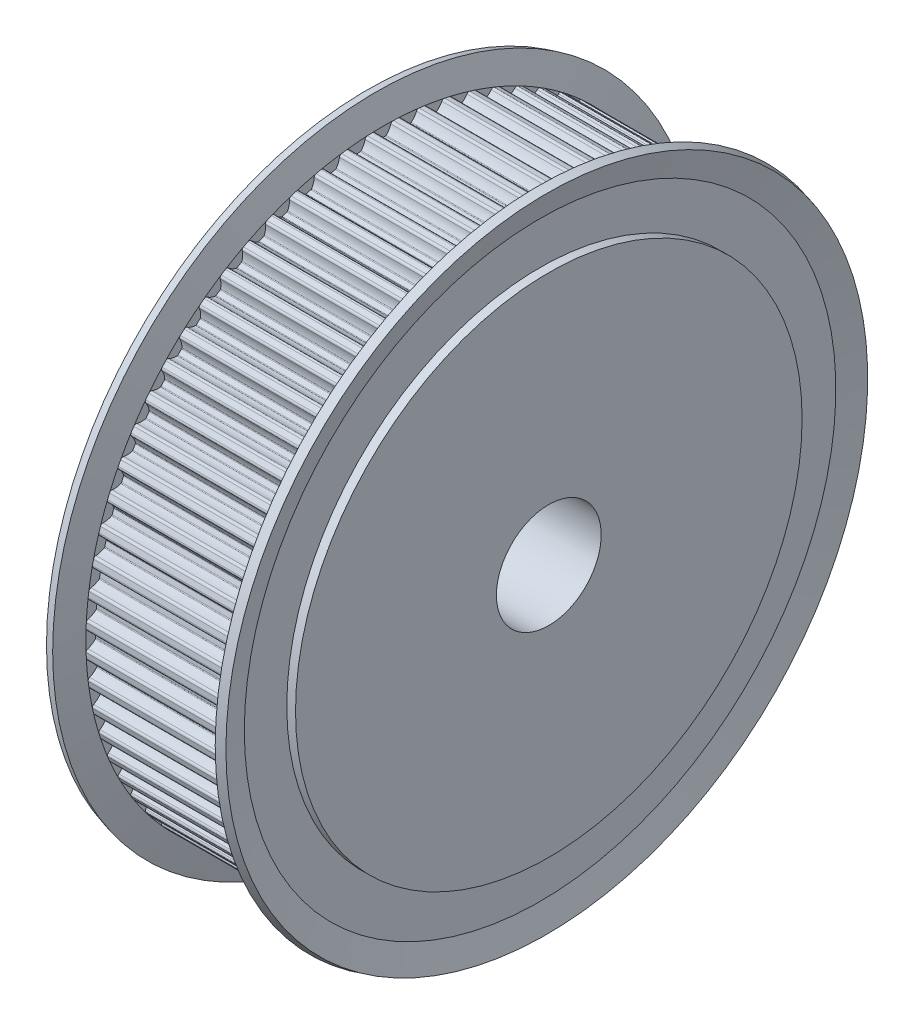
SolidWorks part; units mm, degrees
ref_plane "正面" through (0, 0, 0) normal (0, 0, 1) x (1, 0, 0)
ref_plane "平面" through (0, 0, 0) normal (0, 1, 0) x (1, 0, 0)
ref_plane "右側面" through (0, 0, 0) normal (1, 0, 0) x (0, 0, -1)
ref_plane "平面1" through (0, 0, 0) normal (0, 0, 1) x (1, 0, 0)
sketch "ｽｹｯﾁ1" plane through (0, 0, 0) normal (0, 0, 1) x (1, 0, 0)
  line L0 (0, 0) -> (0, 29)
  line L1 (0, 29) -> (1, 29)
  line L2 (1, 29) -> (1, 33.8633)
  line L3 (1, 33.8633) -> (0.2289, 36.7412)
  line L4 (0.2289, 36.7412) -> (1.1948, 37)
  line L5 (1.1948, 37) -> (2, 33.995)
  line L6 (2, 33.995) -> (19, 33.995)
  line L7 (19, 33.995) -> (19.8052, 37)
  line L8 (19.8052, 37) -> (20.7711, 36.7412)
  line L9 (20.7711, 36.7412) -> (20, 33.8633)
  line L10 (20, 33.8633) -> (20, 29)
  line L11 (20, 29) -> (21, 29)
  line L12 (21, 29) -> (21, 0)
  line L13 (21, 0) -> (0, 0)
  line L14 (21, 0) -> (0, 0) construction
revolve "回転1" add sketch "ｽｹｯﾁ1" angle 360 about L14
ref_plane "平面2" through (0, 0, 0) normal (0, 0, 1) x (1, 0, 0)
sketch "ｽｹｯﾁ2" plane through (0, 0, 0) normal (0, 0, 1) x (1, 0, 0)
  line L0 (0, 0) -> (0, 6)
  line L1 (0, 6) -> (21, 6)
  line L2 (21, 6) -> (21, 0)
  line L3 (21, 0) -> (0, 0)
  line L4 (21, 0) -> (0, 0) construction
revolve "ｶｯﾄ - 回転1" cut sketch "ｽｹｯﾁ2" angle 360 about L4
ref_plane "平面3" through (2, 0, 0) normal (1, 0, 0) x (0, 0, -1)
sketch "ｽｹｯﾁ3" plane through (2, 0, 0) normal (1, 0, 0) x (0, 0, -1)
  circle A0 centre (0, 0) radius 38.995
  arc A1 (-33.7772, -0.9117) -> (-33.9742, -1.189) centre (-33.6944, -1.1792) ccw
  arc A2 (-33.9742, -1.189) -> (-33.9485, -1.7766) centre (0, 0) ccw
  arc A3 (-33.9485, -1.7766) -> (-33.7281, -2.0357) centre (-33.6689, -1.762) ccw
  arc A4 (-33.7281, -2.0357) -> (-32.8326, -2.4906) centre (-34.1454, -3.9661) cw
  arc A5 (-32.8326, -2.4906) -> (-32.7828, -2.5908) centre (-32.9323, -2.6026) cw
  arc A6 (-32.7828, -2.5908) -> (-32.7346, -3.1412) centre (0, 0) ccw
  arc A7 (-32.7346, -3.1412) -> (-32.7663, -3.2486) centre (-32.8839, -3.1556) cw
  arc A8 (-32.7663, -3.2486) -> (-33.5692, -3.8521) centre (-34.3154, -2.0235) cw
  arc A9 (-33.5692, -3.8521) -> (-33.7413, -4.1455) centre (-33.4634, -4.1113) ccw
  arc A10 (-33.7413, -4.1455) -> (-33.6645, -4.7287) centre (0, 0) ccw
  arc A11 (-33.6645, -4.7287) -> (-33.4223, -4.9675) centre (-33.3872, -4.6897) ccw
  arc A12 (-33.4223, -4.9675) -> (-32.4906, -5.3426) centre (-33.6698, -6.9269) cw
  arc A13 (-32.4906, -5.3426) -> (-32.4322, -5.4382) centre (-32.5802, -5.463) cw
  arc A14 (-32.4322, -5.4382) -> (-32.3363, -5.9823) centre (0, 0) ccw
  arc A15 (-32.3363, -5.9823) -> (-32.3585, -6.092) centre (-32.4838, -6.0096) cw
  arc A16 (-32.3585, -6.092) -> (-33.1057, -6.7632) centre (-34.0085, -5.0066) cw
  arc A17 (-33.1057, -6.7632) -> (-33.2516, -7.0704) centre (-32.9777, -7.0122) ccw
  arc A18 (-33.2516, -7.0704) -> (-33.1243, -7.6447) centre (0, 0) ccw
  arc A19 (-33.1243, -7.6447) -> (-32.8622, -7.8616) centre (-32.8515, -7.5818) ccw
  arc A20 (-32.8622, -7.8616) -> (-31.9013, -8.154) centre (-32.938, -9.8351) cw
  arc A21 (-31.9013, -8.154) -> (-31.8349, -8.2441) centre (-31.9801, -8.2817) cw
  arc A22 (-31.8349, -8.2441) -> (-31.6918, -8.7778) centre (0, 0) ccw
  arc A23 (-31.6918, -8.7778) -> (-31.7044, -8.8891) centre (-31.8364, -8.8178) cw
  arc A24 (-31.7044, -8.8891) -> (-32.3903, -9.6228) centre (-33.4427, -7.9515) cw
  arc A25 (-32.3903, -9.6228) -> (-32.5088, -9.9416) centre (-32.2411, -9.8597) ccw
  arc A26 (-32.5088, -9.9416) -> (-32.332, -10.5026) centre (0, 0) ccw
  arc A27 (-32.332, -10.5026) -> (-32.052, -10.6958) centre (-32.0657, -10.4161) ccw
  arc A28 (-32.052, -10.6958) -> (-31.0693, -10.9034) centre (-31.9555, -12.6684) cw
  arc A29 (-31.0693, -10.9034) -> (-30.9952, -10.9873) centre (-31.1366, -11.0375) cw
  arc A30 (-30.9952, -10.9873) -> (-30.8062, -11.5065) centre (0, 0) ccw
  arc A31 (-30.8062, -11.5065) -> (-30.809, -11.6184) centre (-30.9467, -11.559) cw
  arc A32 (-30.809, -11.6184) -> (-31.4283, -12.4092) centre (-32.6224, -10.836) cw
  arc A33 (-31.4283, -12.4092) -> (-31.5187, -12.7371) centre (-31.2591, -12.6322) ccw
  arc A34 (-31.5187, -12.7371) -> (-31.2936, -13.2806) centre (0, 0) ccw
  arc A35 (-31.2936, -13.2806) -> (-30.9978, -13.4486) centre (-31.0358, -13.1712) ccw
  arc A36 (-30.9978, -13.4486) -> (-30.0007, -13.5698) centre (-30.7297, -15.4053) cw
  arc A37 (-30.0007, -13.5698) -> (-29.9196, -13.6469) centre (-30.0561, -13.7092) cw
  arc A38 (-29.9196, -13.6469) -> (-29.6861, -14.1477) centre (0, 0) ccw
  arc A39 (-29.6861, -14.1477) -> (-29.6792, -14.2594) centre (-29.8215, -14.2122) cw
  arc A40 (-29.6792, -14.2594) -> (-30.2272, -15.1011) centre (-31.5538, -13.638) cw
  arc A41 (-30.2272, -15.1011) -> (-30.2886, -15.4357) centre (-30.0391, -15.3085) ccw
  arc A42 (-30.2886, -15.4357) -> (-30.017, -15.9574) centre (0, 0) ccw
  arc A43 (-30.017, -15.9574) -> (-29.7077, -16.099) centre (-29.7698, -15.826) ccw
  arc A44 (-29.7077, -16.099) -> (-28.7039, -16.1329) centre (-29.2701, -18.025) cw
  arc A45 (-28.7039, -16.1329) -> (-28.6164, -16.2027) centre (-28.7469, -16.2766) cw
  arc A46 (-28.6164, -16.2027) -> (-28.3401, -16.6812) centre (0, 0) ccw
  arc A47 (-28.3401, -16.6812) -> (-28.3234, -16.7919) centre (-28.4694, -16.7573) cw
  arc A48 (-28.3234, -16.7919) -> (-28.796, -17.6781) centre (-30.2451, -16.3362) cw
  arc A49 (-28.796, -17.6781) -> (-28.828, -18.0168) centre (-28.5906, -17.8684) ccw
  arc A50 (-28.828, -18.0168) -> (-28.512, -18.5129) centre (0, 0) ccw
  arc A51 (-28.512, -18.5129) -> (-28.1916, -18.627) centre (-28.2772, -18.3604) ccw
  arc A52 (-28.1916, -18.627) -> (-27.1886, -18.5732) centre (-27.5878, -20.5074) cw
  arc A53 (-27.1886, -18.5732) -> (-27.0953, -18.6351) centre (-27.2189, -18.7201) cw
  arc A54 (-27.0953, -18.6351) -> (-26.7784, -19.0877) centre (0, 0) ccw
  arc A55 (-26.7784, -19.0877) -> (-26.7521, -19.1965) centre (-26.9006, -19.1748) cw
  arc A56 (-26.7521, -19.1965) -> (-27.1457, -20.1206) centre (-28.7063, -18.9101) cw
  arc A57 (-27.1457, -20.1206) -> (-27.1481, -20.4607) centre (-26.9245, -20.2922) ccw
  arc A58 (-27.1481, -20.4607) -> (-26.79, -20.9274) centre (0, 0) ccw
  arc A59 (-26.79, -20.9274) -> (-26.4608, -21.0132) centre (-26.5693, -20.755) ccw
  arc A60 (-26.4608, -21.0132) -> (-25.4664, -20.8722) centre (-25.6955, -22.8338) cw
  arc A61 (-25.4664, -20.8722) -> (-25.3681, -20.9257) centre (-25.4838, -21.0211) cw
  arc A62 (-25.3681, -20.9257) -> (-25.0129, -21.349) centre (0, 0) ccw
  arc A63 (-25.0129, -21.349) -> (-24.9773, -21.4551) centre (-25.127, -21.4463) cw
  arc A64 (-24.9773, -21.4551) -> (-25.2888, -22.4099) centre (-26.9489, -21.34) cw
  arc A65 (-25.2888, -22.4099) -> (-25.2615, -22.749) centre (-25.0534, -22.5616) ccw
  arc A66 (-25.2615, -22.749) -> (-24.8641, -23.1827) centre (0, 0) ccw
  arc A67 (-24.8641, -23.1827) -> (-24.5287, -23.2394) centre (-24.6593, -22.9917) ccw
  arc A68 (-24.5287, -23.2394) -> (-23.5503, -23.0123) centre (-23.6076, -24.9864) cw
  arc A69 (-23.5503, -23.0123) -> (-23.4477, -23.057) centre (-23.5547, -23.1622) cw
  arc A70 (-23.4477, -23.057) -> (-23.057, -23.4477) centre (0, 0) ccw
  arc A71 (-23.057, -23.4477) -> (-23.0123, -23.5503) centre (-23.1622, -23.5547) cw
  arc A72 (-23.0123, -23.5503) -> (-23.2394, -24.5287) centre (-24.9864, -23.6076) cw
  arc A73 (-23.2394, -24.5287) -> (-23.1827, -24.8641) centre (-22.9917, -24.6593) ccw
  arc A74 (-23.1827, -24.8641) -> (-22.749, -25.2615) centre (0, 0) ccw
  arc A75 (-22.749, -25.2615) -> (-22.4099, -25.2888) centre (-22.5616, -25.0534) ccw
  arc A76 (-22.4099, -25.2888) -> (-21.4551, -24.9773) centre (-21.34, -26.9489) cw
  arc A77 (-21.4551, -24.9773) -> (-21.349, -25.0129) centre (-21.4463, -25.127) cw
  arc A78 (-21.349, -25.0129) -> (-20.9257, -25.3681) centre (0, 0) ccw
  arc A79 (-20.9257, -25.3681) -> (-20.8722, -25.4664) centre (-21.0211, -25.4838) cw
  arc A80 (-20.8722, -25.4664) -> (-21.0132, -26.4608) centre (-22.8338, -25.6955) cw
  arc A81 (-21.0132, -26.4608) -> (-20.9274, -26.79) centre (-20.755, -26.5693) ccw
  arc A82 (-20.9274, -26.79) -> (-20.4607, -27.1481) centre (0, 0) ccw
  arc A83 (-20.4607, -27.1481) -> (-20.1206, -27.1457) centre (-20.2922, -26.9245) ccw
  arc A84 (-20.1206, -27.1457) -> (-19.1965, -26.7521) centre (-18.9101, -28.7063) cw
  arc A85 (-19.1965, -26.7521) -> (-19.0877, -26.7784) centre (-19.1748, -26.9006) cw
  arc A86 (-19.0877, -26.7784) -> (-18.6351, -27.0953) centre (0, 0) ccw
  arc A87 (-18.6351, -27.0953) -> (-18.5732, -27.1886) centre (-18.7201, -27.2189) cw
  arc A88 (-18.5732, -27.1886) -> (-18.627, -28.1916) centre (-20.5074, -27.5878) cw
  arc A89 (-18.627, -28.1916) -> (-18.5129, -28.512) centre (-18.3604, -28.2772) ccw
  arc A90 (-18.5129, -28.512) -> (-18.0168, -28.828) centre (0, 0) ccw
  arc A91 (-18.0168, -28.828) -> (-17.6781, -28.796) centre (-17.8684, -28.5906) ccw
  arc A92 (-17.6781, -28.796) -> (-16.7919, -28.3234) centre (-16.3362, -30.2451) cw
  arc A93 (-16.7919, -28.3234) -> (-16.6812, -28.3401) centre (-16.7573, -28.4694) cw
  arc A94 (-16.6812, -28.3401) -> (-16.2027, -28.6164) centre (0, 0) ccw
  arc A95 (-16.2027, -28.6164) -> (-16.1329, -28.7039) centre (-16.2766, -28.7469) cw
  arc A96 (-16.1329, -28.7039) -> (-16.099, -29.7077) centre (-18.025, -29.2701) cw
  arc A97 (-16.099, -29.7077) -> (-15.9574, -30.017) centre (-15.826, -29.7698) ccw
  arc A98 (-15.9574, -30.017) -> (-15.4357, -30.2886) centre (0, 0) ccw
  arc A99 (-15.4357, -30.2886) -> (-15.1011, -30.2272) centre (-15.3085, -30.0391) ccw
  arc A100 (-15.1011, -30.2272) -> (-14.2594, -29.6792) centre (-13.638, -31.5538) cw
  arc A101 (-14.2594, -29.6792) -> (-14.1477, -29.6861) centre (-14.2122, -29.8215) cw
  arc A102 (-14.1477, -29.6861) -> (-13.6469, -29.9196) centre (0, 0) ccw
  arc A103 (-13.6469, -29.9196) -> (-13.5698, -30.0007) centre (-13.7092, -30.0561) cw
  arc A104 (-13.5698, -30.0007) -> (-13.4486, -30.9978) centre (-15.4053, -30.7297) cw
  arc A105 (-13.4486, -30.9978) -> (-13.2806, -31.2936) centre (-13.1712, -31.0358) ccw
  arc A106 (-13.2806, -31.2936) -> (-12.7371, -31.5187) centre (0, 0) ccw
  arc A107 (-12.7371, -31.5187) -> (-12.4092, -31.4283) centre (-12.6322, -31.2591) ccw
  arc A108 (-12.4092, -31.4283) -> (-11.6184, -30.809) centre (-10.836, -32.6224) cw
  arc A109 (-11.6184, -30.809) -> (-11.5065, -30.8062) centre (-11.559, -30.9467) cw
  arc A110 (-11.5065, -30.8062) -> (-10.9873, -30.9952) centre (0, 0) ccw
  arc A111 (-10.9873, -30.9952) -> (-10.9034, -31.0693) centre (-11.0375, -31.1366) cw
  arc A112 (-10.9034, -31.0693) -> (-10.6958, -32.052) centre (-12.6684, -31.9555) cw
  arc A113 (-10.6958, -32.052) -> (-10.5026, -32.332) centre (-10.4161, -32.0657) ccw
  arc A114 (-10.5026, -32.332) -> (-9.9416, -32.5088) centre (0, 0) ccw
  arc A115 (-9.9416, -32.5088) -> (-9.6228, -32.3903) centre (-9.8597, -32.2411) ccw
  arc A116 (-9.6228, -32.3903) -> (-8.8891, -31.7044) centre (-7.9515, -33.4427) cw
  arc A117 (-8.8891, -31.7044) -> (-8.7778, -31.6918) centre (-8.8178, -31.8364) cw
  arc A118 (-8.7778, -31.6918) -> (-8.2441, -31.8349) centre (0, 0) ccw
  arc A119 (-8.2441, -31.8349) -> (-8.154, -31.9013) centre (-8.2817, -31.9801) cw
  arc A120 (-8.154, -31.9013) -> (-7.8616, -32.8622) centre (-9.8351, -32.938) cw
  arc A121 (-7.8616, -32.8622) -> (-7.6447, -33.1243) centre (-7.5818, -32.8515) ccw
  arc A122 (-7.6447, -33.1243) -> (-7.0704, -33.2516) centre (0, 0) ccw
  arc A123 (-7.0704, -33.2516) -> (-6.7632, -33.1057) centre (-7.0122, -32.9777) ccw
  arc A124 (-6.7632, -33.1057) -> (-6.092, -32.3585) centre (-5.0066, -34.0085) cw
  arc A125 (-6.092, -32.3585) -> (-5.9823, -32.3363) centre (-6.0096, -32.4838) cw
  arc A126 (-5.9823, -32.3363) -> (-5.4382, -32.4322) centre (0, 0) ccw
  arc A127 (-5.4382, -32.4322) -> (-5.3426, -32.4906) centre (-5.463, -32.5802) cw
  arc A128 (-5.3426, -32.4906) -> (-4.9675, -33.4223) centre (-6.9269, -33.6698) cw
  arc A129 (-4.9675, -33.4223) -> (-4.7287, -33.6645) centre (-4.6897, -33.3872) ccw
  arc A130 (-4.7287, -33.6645) -> (-4.1455, -33.7413) centre (0, 0) ccw
  arc A131 (-4.1455, -33.7413) -> (-3.8521, -33.5692) centre (-4.1113, -33.4634) ccw
  arc A132 (-3.8521, -33.5692) -> (-3.2486, -32.7663) centre (-2.0235, -34.3154) cw
  arc A133 (-3.2486, -32.7663) -> (-3.1412, -32.7346) centre (-3.1556, -32.8839) cw
  arc A134 (-3.1412, -32.7346) -> (-2.5908, -32.7828) centre (0, 0) ccw
  arc A135 (-2.5908, -32.7828) -> (-2.4906, -32.8326) centre (-2.6026, -32.9323) cw
  arc A136 (-2.4906, -32.8326) -> (-2.0357, -33.7281) centre (-3.9661, -34.1454) cw
  arc A137 (-2.0357, -33.7281) -> (-1.7766, -33.9485) centre (-1.762, -33.6689) ccw
  arc A138 (-1.7766, -33.9485) -> (-1.189, -33.9742) centre (0, 0) ccw
  arc A139 (-1.189, -33.9742) -> (-0.9117, -33.7772) centre (-1.1792, -33.6944) ccw
  arc A140 (-0.9117, -33.7772) -> (-0.3805, -32.9247) centre (0.975, -34.3612) cw
  arc A141 (-0.3805, -32.9247) -> (-0.2763, -32.8838) centre (-0.2775, -33.0338) cw
  arc A142 (-0.2763, -32.8838) -> (0.2763, -32.8838) centre (0, 0) ccw
  arc A143 (0.2763, -32.8838) -> (0.3805, -32.9247) centre (0.2775, -33.0338) cw
  arc A144 (0.3805, -32.9247) -> (0.9117, -33.7772) centre (-0.975, -34.3612) cw
  arc A145 (0.9117, -33.7772) -> (1.189, -33.9742) centre (1.1792, -33.6944) ccw
  arc A146 (1.189, -33.9742) -> (1.7766, -33.9485) centre (0, 0) ccw
  arc A147 (1.7766, -33.9485) -> (2.0357, -33.7281) centre (1.762, -33.6689) ccw
  arc A148 (2.0357, -33.7281) -> (2.4906, -32.8326) centre (3.9661, -34.1454) cw
  arc A149 (2.4906, -32.8326) -> (2.5908, -32.7828) centre (2.6026, -32.9323) cw
  arc A150 (2.5908, -32.7828) -> (3.1412, -32.7346) centre (0, 0) ccw
  arc A151 (3.1412, -32.7346) -> (3.2486, -32.7663) centre (3.1556, -32.8839) cw
  arc A152 (3.2486, -32.7663) -> (3.8521, -33.5692) centre (2.0235, -34.3154) cw
  arc A153 (3.8521, -33.5692) -> (4.1455, -33.7413) centre (4.1113, -33.4634) ccw
  arc A154 (4.1455, -33.7413) -> (4.7287, -33.6645) centre (0, 0) ccw
  arc A155 (4.7287, -33.6645) -> (4.9675, -33.4223) centre (4.6897, -33.3872) ccw
  arc A156 (4.9675, -33.4223) -> (5.3426, -32.4906) centre (6.9269, -33.6698) cw
  arc A157 (5.3426, -32.4906) -> (5.4382, -32.4322) centre (5.463, -32.5802) cw
  arc A158 (5.4382, -32.4322) -> (5.9823, -32.3363) centre (0, 0) ccw
  arc A159 (5.9823, -32.3363) -> (6.092, -32.3585) centre (6.0096, -32.4838) cw
  arc A160 (6.092, -32.3585) -> (6.7632, -33.1057) centre (5.0066, -34.0085) cw
  arc A161 (6.7632, -33.1057) -> (7.0704, -33.2516) centre (7.0122, -32.9777) ccw
  arc A162 (7.0704, -33.2516) -> (7.6447, -33.1243) centre (0, 0) ccw
  arc A163 (7.6447, -33.1243) -> (7.8616, -32.8622) centre (7.5818, -32.8515) ccw
  arc A164 (7.8616, -32.8622) -> (8.154, -31.9013) centre (9.8351, -32.938) cw
  arc A165 (8.154, -31.9013) -> (8.2441, -31.8349) centre (8.2817, -31.9801) cw
  arc A166 (8.2441, -31.8349) -> (8.7778, -31.6918) centre (0, 0) ccw
  arc A167 (8.7778, -31.6918) -> (8.8891, -31.7044) centre (8.8178, -31.8364) cw
  arc A168 (8.8891, -31.7044) -> (9.6228, -32.3903) centre (7.9515, -33.4427) cw
  arc A169 (9.6228, -32.3903) -> (9.9416, -32.5088) centre (9.8597, -32.2411) ccw
  arc A170 (9.9416, -32.5088) -> (10.5026, -32.332) centre (0, 0) ccw
  arc A171 (10.5026, -32.332) -> (10.6958, -32.052) centre (10.4161, -32.0657) ccw
  arc A172 (10.6958, -32.052) -> (10.9034, -31.0693) centre (12.6684, -31.9555) cw
  arc A173 (10.9034, -31.0693) -> (10.9873, -30.9952) centre (11.0375, -31.1366) cw
  arc A174 (10.9873, -30.9952) -> (11.5065, -30.8062) centre (0, 0) ccw
  arc A175 (11.5065, -30.8062) -> (11.6184, -30.809) centre (11.559, -30.9467) cw
  arc A176 (11.6184, -30.809) -> (12.4092, -31.4283) centre (10.836, -32.6224) cw
  arc A177 (12.4092, -31.4283) -> (12.7371, -31.5187) centre (12.6322, -31.2591) ccw
  arc A178 (12.7371, -31.5187) -> (13.2806, -31.2936) centre (0, 0) ccw
  arc A179 (13.2806, -31.2936) -> (13.4486, -30.9978) centre (13.1712, -31.0358) ccw
  arc A180 (13.4486, -30.9978) -> (13.5698, -30.0007) centre (15.4053, -30.7297) cw
  arc A181 (13.5698, -30.0007) -> (13.6469, -29.9196) centre (13.7092, -30.0561) cw
  arc A182 (13.6469, -29.9196) -> (14.1477, -29.6861) centre (0, 0) ccw
  arc A183 (14.1477, -29.6861) -> (14.2594, -29.6792) centre (14.2122, -29.8215) cw
  arc A184 (14.2594, -29.6792) -> (15.1011, -30.2272) centre (13.638, -31.5538) cw
  arc A185 (15.1011, -30.2272) -> (15.4357, -30.2886) centre (15.3085, -30.0391) ccw
  arc A186 (15.4357, -30.2886) -> (15.9574, -30.017) centre (0, 0) ccw
  arc A187 (15.9574, -30.017) -> (16.099, -29.7077) centre (15.826, -29.7698) ccw
  arc A188 (16.099, -29.7077) -> (16.1329, -28.7039) centre (18.025, -29.2701) cw
  arc A189 (16.1329, -28.7039) -> (16.2027, -28.6164) centre (16.2766, -28.7469) cw
  arc A190 (16.2027, -28.6164) -> (16.6812, -28.3401) centre (0, 0) ccw
  arc A191 (16.6812, -28.3401) -> (16.7919, -28.3234) centre (16.7573, -28.4694) cw
  arc A192 (16.7919, -28.3234) -> (17.6781, -28.796) centre (16.3362, -30.2451) cw
  arc A193 (17.6781, -28.796) -> (18.0168, -28.828) centre (17.8684, -28.5906) ccw
  arc A194 (18.0168, -28.828) -> (18.5129, -28.512) centre (0, 0) ccw
  arc A195 (18.5129, -28.512) -> (18.627, -28.1916) centre (18.3604, -28.2772) ccw
  arc A196 (18.627, -28.1916) -> (18.5732, -27.1886) centre (20.5074, -27.5878) cw
  arc A197 (18.5732, -27.1886) -> (18.6351, -27.0953) centre (18.7201, -27.2189) cw
  arc A198 (18.6351, -27.0953) -> (19.0877, -26.7784) centre (0, 0) ccw
  arc A199 (19.0877, -26.7784) -> (19.1965, -26.7521) centre (19.1748, -26.9006) cw
  arc A200 (19.1965, -26.7521) -> (20.1206, -27.1457) centre (18.9101, -28.7063) cw
  arc A201 (20.1206, -27.1457) -> (20.4607, -27.1481) centre (20.2922, -26.9245) ccw
  arc A202 (20.4607, -27.1481) -> (20.9274, -26.79) centre (0, 0) ccw
  arc A203 (20.9274, -26.79) -> (21.0132, -26.4608) centre (20.755, -26.5693) ccw
  arc A204 (21.0132, -26.4608) -> (20.8722, -25.4664) centre (22.8338, -25.6955) cw
  arc A205 (20.8722, -25.4664) -> (20.9257, -25.3681) centre (21.0211, -25.4838) cw
  arc A206 (20.9257, -25.3681) -> (21.349, -25.0129) centre (0, 0) ccw
  arc A207 (21.349, -25.0129) -> (21.4551, -24.9773) centre (21.4463, -25.127) cw
  arc A208 (21.4551, -24.9773) -> (22.4099, -25.2888) centre (21.34, -26.9489) cw
  arc A209 (22.4099, -25.2888) -> (22.749, -25.2615) centre (22.5616, -25.0534) ccw
  arc A210 (22.749, -25.2615) -> (23.1827, -24.8641) centre (0, 0) ccw
  arc A211 (23.1827, -24.8641) -> (23.2394, -24.5287) centre (22.9917, -24.6593) ccw
  arc A212 (23.2394, -24.5287) -> (23.0123, -23.5503) centre (24.9864, -23.6076) cw
  arc A213 (23.0123, -23.5503) -> (23.057, -23.4477) centre (23.1622, -23.5547) cw
  arc A214 (23.057, -23.4477) -> (23.4477, -23.057) centre (0, 0) ccw
  arc A215 (23.4477, -23.057) -> (23.5503, -23.0123) centre (23.5547, -23.1622) cw
  arc A216 (23.5503, -23.0123) -> (24.5287, -23.2394) centre (23.6076, -24.9864) cw
  arc A217 (24.5287, -23.2394) -> (24.8641, -23.1827) centre (24.6593, -22.9917) ccw
  arc A218 (24.8641, -23.1827) -> (25.2615, -22.749) centre (0, 0) ccw
  arc A219 (25.2615, -22.749) -> (25.2888, -22.4099) centre (25.0534, -22.5616) ccw
  arc A220 (25.2888, -22.4099) -> (24.9773, -21.4551) centre (26.9489, -21.34) cw
  arc A221 (24.9773, -21.4551) -> (25.0129, -21.349) centre (25.127, -21.4463) cw
  arc A222 (25.0129, -21.349) -> (25.3681, -20.9257) centre (0, 0) ccw
  arc A223 (25.3681, -20.9257) -> (25.4664, -20.8722) centre (25.4838, -21.0211) cw
  arc A224 (25.4664, -20.8722) -> (26.4608, -21.0132) centre (25.6955, -22.8338) cw
  arc A225 (26.4608, -21.0132) -> (26.79, -20.9274) centre (26.5693, -20.755) ccw
  arc A226 (26.79, -20.9274) -> (27.1481, -20.4607) centre (0, 0) ccw
  arc A227 (27.1481, -20.4607) -> (27.1457, -20.1206) centre (26.9245, -20.2922) ccw
  arc A228 (27.1457, -20.1206) -> (26.7521, -19.1965) centre (28.7063, -18.9101) cw
  arc A229 (26.7521, -19.1965) -> (26.7784, -19.0877) centre (26.9006, -19.1748) cw
  arc A230 (26.7784, -19.0877) -> (27.0953, -18.6351) centre (0, 0) ccw
  arc A231 (27.0953, -18.6351) -> (27.1886, -18.5732) centre (27.2189, -18.7201) cw
  arc A232 (27.1886, -18.5732) -> (28.1916, -18.627) centre (27.5878, -20.5074) cw
  arc A233 (28.1916, -18.627) -> (28.512, -18.5129) centre (28.2772, -18.3604) ccw
  arc A234 (28.512, -18.5129) -> (28.828, -18.0168) centre (0, 0) ccw
  arc A235 (28.828, -18.0168) -> (28.796, -17.6781) centre (28.5906, -17.8684) ccw
  arc A236 (28.796, -17.6781) -> (28.3234, -16.7919) centre (30.2451, -16.3362) cw
  arc A237 (28.3234, -16.7919) -> (28.3401, -16.6812) centre (28.4694, -16.7573) cw
  arc A238 (28.3401, -16.6812) -> (28.6164, -16.2027) centre (0, 0) ccw
  arc A239 (28.6164, -16.2027) -> (28.7039, -16.1329) centre (28.7469, -16.2766) cw
  arc A240 (28.7039, -16.1329) -> (29.7077, -16.099) centre (29.2701, -18.025) cw
  arc A241 (29.7077, -16.099) -> (30.017, -15.9574) centre (29.7698, -15.826) ccw
  arc A242 (30.017, -15.9574) -> (30.2886, -15.4357) centre (0, 0) ccw
  arc A243 (30.2886, -15.4357) -> (30.2272, -15.1011) centre (30.0391, -15.3085) ccw
  arc A244 (30.2272, -15.1011) -> (29.6792, -14.2594) centre (31.5538, -13.638) cw
  arc A245 (29.6792, -14.2594) -> (29.6861, -14.1477) centre (29.8215, -14.2122) cw
  arc A246 (29.6861, -14.1477) -> (29.9196, -13.6469) centre (0, 0) ccw
  arc A247 (29.9196, -13.6469) -> (30.0007, -13.5698) centre (30.0561, -13.7092) cw
  arc A248 (30.0007, -13.5698) -> (30.9978, -13.4486) centre (30.7297, -15.4053) cw
  arc A249 (30.9978, -13.4486) -> (31.2936, -13.2806) centre (31.0358, -13.1712) ccw
  arc A250 (31.2936, -13.2806) -> (31.5187, -12.7371) centre (0, 0) ccw
  arc A251 (31.5187, -12.7371) -> (31.4283, -12.4092) centre (31.2591, -12.6322) ccw
  arc A252 (31.4283, -12.4092) -> (30.809, -11.6184) centre (32.6224, -10.836) cw
  arc A253 (30.809, -11.6184) -> (30.8062, -11.5065) centre (30.9467, -11.559) cw
  arc A254 (30.8062, -11.5065) -> (30.9952, -10.9873) centre (0, 0) ccw
  arc A255 (30.9952, -10.9873) -> (31.0693, -10.9034) centre (31.1366, -11.0375) cw
  arc A256 (31.0693, -10.9034) -> (32.052, -10.6958) centre (31.9555, -12.6684) cw
  arc A257 (32.052, -10.6958) -> (32.332, -10.5026) centre (32.0657, -10.4161) ccw
  arc A258 (32.332, -10.5026) -> (32.5088, -9.9416) centre (0, 0) ccw
  arc A259 (32.5088, -9.9416) -> (32.3903, -9.6228) centre (32.2411, -9.8597) ccw
  arc A260 (32.3903, -9.6228) -> (31.7044, -8.8891) centre (33.4427, -7.9515) cw
  arc A261 (31.7044, -8.8891) -> (31.6918, -8.7778) centre (31.8364, -8.8178) cw
  arc A262 (31.6918, -8.7778) -> (31.8349, -8.2441) centre (0, 0) ccw
  arc A263 (31.8349, -8.2441) -> (31.9013, -8.154) centre (31.9801, -8.2817) cw
  arc A264 (31.9013, -8.154) -> (32.8622, -7.8616) centre (32.938, -9.8351) cw
  arc A265 (32.8622, -7.8616) -> (33.1243, -7.6447) centre (32.8515, -7.5818) ccw
  arc A266 (33.1243, -7.6447) -> (33.2516, -7.0704) centre (0, 0) ccw
  arc A267 (33.2516, -7.0704) -> (33.1057, -6.7632) centre (32.9777, -7.0122) ccw
  arc A268 (33.1057, -6.7632) -> (32.3585, -6.092) centre (34.0085, -5.0066) cw
  arc A269 (32.3585, -6.092) -> (32.3363, -5.9823) centre (32.4838, -6.0096) cw
  arc A270 (32.3363, -5.9823) -> (32.4322, -5.4382) centre (0, 0) ccw
  arc A271 (32.4322, -5.4382) -> (32.4906, -5.3426) centre (32.5802, -5.463) cw
  arc A272 (32.4906, -5.3426) -> (33.4223, -4.9675) centre (33.6698, -6.9269) cw
  arc A273 (33.4223, -4.9675) -> (33.6645, -4.7287) centre (33.3872, -4.6897) ccw
  arc A274 (33.6645, -4.7287) -> (33.7413, -4.1455) centre (0, 0) ccw
  arc A275 (33.7413, -4.1455) -> (33.5692, -3.8521) centre (33.4634, -4.1113) ccw
  arc A276 (33.5692, -3.8521) -> (32.7663, -3.2486) centre (34.3154, -2.0235) cw
  arc A277 (32.7663, -3.2486) -> (32.7346, -3.1412) centre (32.8839, -3.1556) cw
  arc A278 (32.7346, -3.1412) -> (32.7828, -2.5908) centre (0, 0) ccw
  arc A279 (32.7828, -2.5908) -> (32.8326, -2.4906) centre (32.9323, -2.6026) cw
  arc A280 (32.8326, -2.4906) -> (33.7281, -2.0357) centre (34.1454, -3.9661) cw
  arc A281 (33.7281, -2.0357) -> (33.9485, -1.7766) centre (33.6689, -1.762) ccw
  arc A282 (33.9485, -1.7766) -> (33.9742, -1.189) centre (0, 0) ccw
  arc A283 (33.9742, -1.189) -> (33.7772, -0.9117) centre (33.6944, -1.1792) ccw
  arc A284 (33.7772, -0.9117) -> (32.9247, -0.3805) centre (34.3612, 0.975) cw
  arc A285 (32.9247, -0.3805) -> (32.8838, -0.2763) centre (33.0338, -0.2775) cw
  arc A286 (32.8838, -0.2763) -> (32.8838, 0.2763) centre (0, 0) ccw
  arc A287 (32.8838, 0.2763) -> (32.9247, 0.3805) centre (33.0338, 0.2775) cw
  arc A288 (32.9247, 0.3805) -> (33.7772, 0.9117) centre (34.3612, -0.975) cw
  arc A289 (33.7772, 0.9117) -> (33.9742, 1.189) centre (33.6944, 1.1792) ccw
  arc A290 (33.9742, 1.189) -> (33.9485, 1.7766) centre (0, 0) ccw
  arc A291 (33.9485, 1.7766) -> (33.7281, 2.0357) centre (33.6689, 1.762) ccw
  arc A292 (33.7281, 2.0357) -> (32.8326, 2.4906) centre (34.1454, 3.9661) cw
  arc A293 (32.8326, 2.4906) -> (32.7828, 2.5908) centre (32.9323, 2.6026) cw
  arc A294 (32.7828, 2.5908) -> (32.7346, 3.1412) centre (0, 0) ccw
  arc A295 (32.7346, 3.1412) -> (32.7663, 3.2486) centre (32.8839, 3.1556) cw
  arc A296 (32.7663, 3.2486) -> (33.5692, 3.8521) centre (34.3154, 2.0235) cw
  arc A297 (33.5692, 3.8521) -> (33.7413, 4.1455) centre (33.4634, 4.1113) ccw
  arc A298 (33.7413, 4.1455) -> (33.6645, 4.7287) centre (0, 0) ccw
  arc A299 (33.6645, 4.7287) -> (33.4223, 4.9675) centre (33.3872, 4.6897) ccw
  arc A300 (33.4223, 4.9675) -> (32.4906, 5.3426) centre (33.6698, 6.9269) cw
  arc A301 (32.4906, 5.3426) -> (32.4322, 5.4382) centre (32.5802, 5.463) cw
  arc A302 (32.4322, 5.4382) -> (32.3363, 5.9823) centre (0, 0) ccw
  arc A303 (32.3363, 5.9823) -> (32.3585, 6.092) centre (32.4838, 6.0096) cw
  arc A304 (32.3585, 6.092) -> (33.1057, 6.7632) centre (34.0085, 5.0066) cw
  arc A305 (33.1057, 6.7632) -> (33.2516, 7.0704) centre (32.9777, 7.0122) ccw
  arc A306 (33.2516, 7.0704) -> (33.1243, 7.6447) centre (0, 0) ccw
  arc A307 (33.1243, 7.6447) -> (32.8622, 7.8616) centre (32.8515, 7.5818) ccw
  arc A308 (32.8622, 7.8616) -> (31.9013, 8.154) centre (32.938, 9.8351) cw
  arc A309 (31.9013, 8.154) -> (31.8349, 8.2441) centre (31.9801, 8.2817) cw
  arc A310 (31.8349, 8.2441) -> (31.6918, 8.7778) centre (0, 0) ccw
  arc A311 (31.6918, 8.7778) -> (31.7044, 8.8891) centre (31.8364, 8.8178) cw
  arc A312 (31.7044, 8.8891) -> (32.3903, 9.6228) centre (33.4427, 7.9515) cw
  arc A313 (32.3903, 9.6228) -> (32.5088, 9.9416) centre (32.2411, 9.8597) ccw
  arc A314 (32.5088, 9.9416) -> (32.332, 10.5026) centre (0, 0) ccw
  arc A315 (32.332, 10.5026) -> (32.052, 10.6958) centre (32.0657, 10.4161) ccw
  arc A316 (32.052, 10.6958) -> (31.0693, 10.9034) centre (31.9555, 12.6684) cw
  arc A317 (31.0693, 10.9034) -> (30.9952, 10.9873) centre (31.1366, 11.0375) cw
  arc A318 (30.9952, 10.9873) -> (30.8062, 11.5065) centre (0, 0) ccw
  arc A319 (30.8062, 11.5065) -> (30.809, 11.6184) centre (30.9467, 11.559) cw
  arc A320 (30.809, 11.6184) -> (31.4283, 12.4092) centre (32.6224, 10.836) cw
  arc A321 (31.4283, 12.4092) -> (31.5187, 12.7371) centre (31.2591, 12.6322) ccw
  arc A322 (31.5187, 12.7371) -> (31.2936, 13.2806) centre (0, 0) ccw
  arc A323 (31.2936, 13.2806) -> (30.9978, 13.4486) centre (31.0358, 13.1712) ccw
  arc A324 (30.9978, 13.4486) -> (30.0007, 13.5698) centre (30.7297, 15.4053) cw
  arc A325 (30.0007, 13.5698) -> (29.9196, 13.6469) centre (30.0561, 13.7092) cw
  arc A326 (29.9196, 13.6469) -> (29.6861, 14.1477) centre (0, 0) ccw
  arc A327 (29.6861, 14.1477) -> (29.6792, 14.2594) centre (29.8215, 14.2122) cw
  arc A328 (29.6792, 14.2594) -> (30.2272, 15.1011) centre (31.5538, 13.638) cw
  arc A329 (30.2272, 15.1011) -> (30.2886, 15.4357) centre (30.0391, 15.3085) ccw
  arc A330 (30.2886, 15.4357) -> (30.017, 15.9574) centre (0, 0) ccw
  arc A331 (30.017, 15.9574) -> (29.7077, 16.099) centre (29.7698, 15.826) ccw
  arc A332 (29.7077, 16.099) -> (28.7039, 16.1329) centre (29.2701, 18.025) cw
  arc A333 (28.7039, 16.1329) -> (28.6164, 16.2027) centre (28.7469, 16.2766) cw
  arc A334 (28.6164, 16.2027) -> (28.3401, 16.6812) centre (0, 0) ccw
  arc A335 (28.3401, 16.6812) -> (28.3234, 16.7919) centre (28.4694, 16.7573) cw
  arc A336 (28.3234, 16.7919) -> (28.796, 17.6781) centre (30.2451, 16.3362) cw
  arc A337 (28.796, 17.6781) -> (28.828, 18.0168) centre (28.5906, 17.8684) ccw
  arc A338 (28.828, 18.0168) -> (28.512, 18.5129) centre (0, 0) ccw
  arc A339 (28.512, 18.5129) -> (28.1916, 18.627) centre (28.2772, 18.3604) ccw
  arc A340 (28.1916, 18.627) -> (27.1886, 18.5732) centre (27.5878, 20.5074) cw
  arc A341 (27.1886, 18.5732) -> (27.0953, 18.6351) centre (27.2189, 18.7201) cw
  arc A342 (27.0953, 18.6351) -> (26.7784, 19.0877) centre (0, 0) ccw
  arc A343 (26.7784, 19.0877) -> (26.7521, 19.1965) centre (26.9006, 19.1748) cw
  arc A344 (26.7521, 19.1965) -> (27.1457, 20.1206) centre (28.7063, 18.9101) cw
  arc A345 (27.1457, 20.1206) -> (27.1481, 20.4607) centre (26.9245, 20.2922) ccw
  arc A346 (27.1481, 20.4607) -> (26.79, 20.9274) centre (0, 0) ccw
  arc A347 (26.79, 20.9274) -> (26.4608, 21.0132) centre (26.5693, 20.755) ccw
  arc A348 (26.4608, 21.0132) -> (25.4664, 20.8722) centre (25.6955, 22.8338) cw
  arc A349 (25.4664, 20.8722) -> (25.3681, 20.9257) centre (25.4838, 21.0211) cw
  arc A350 (25.3681, 20.9257) -> (25.0129, 21.349) centre (0, 0) ccw
  arc A351 (25.0129, 21.349) -> (24.9773, 21.4551) centre (25.127, 21.4463) cw
  arc A352 (24.9773, 21.4551) -> (25.2888, 22.4099) centre (26.9489, 21.34) cw
  arc A353 (25.2888, 22.4099) -> (25.2615, 22.749) centre (25.0534, 22.5616) ccw
  arc A354 (25.2615, 22.749) -> (24.8641, 23.1827) centre (0, 0) ccw
  arc A355 (24.8641, 23.1827) -> (24.5287, 23.2394) centre (24.6593, 22.9917) ccw
  arc A356 (24.5287, 23.2394) -> (23.5503, 23.0123) centre (23.6076, 24.9864) cw
  arc A357 (23.5503, 23.0123) -> (23.4477, 23.057) centre (23.5547, 23.1622) cw
  arc A358 (23.4477, 23.057) -> (23.057, 23.4477) centre (0, 0) ccw
  arc A359 (23.057, 23.4477) -> (23.0123, 23.5503) centre (23.1622, 23.5547) cw
  arc A360 (23.0123, 23.5503) -> (23.2394, 24.5287) centre (24.9864, 23.6076) cw
  arc A361 (23.2394, 24.5287) -> (23.1827, 24.8641) centre (22.9917, 24.6593) ccw
  arc A362 (23.1827, 24.8641) -> (22.749, 25.2615) centre (0, 0) ccw
  arc A363 (22.749, 25.2615) -> (22.4099, 25.2888) centre (22.5616, 25.0534) ccw
  arc A364 (22.4099, 25.2888) -> (21.4551, 24.9773) centre (21.34, 26.9489) cw
  arc A365 (21.4551, 24.9773) -> (21.349, 25.0129) centre (21.4463, 25.127) cw
  arc A366 (21.349, 25.0129) -> (20.9257, 25.3681) centre (0, 0) ccw
  arc A367 (20.9257, 25.3681) -> (20.8722, 25.4664) centre (21.0211, 25.4838) cw
  arc A368 (20.8722, 25.4664) -> (21.0132, 26.4608) centre (22.8338, 25.6955) cw
  arc A369 (21.0132, 26.4608) -> (20.9274, 26.79) centre (20.755, 26.5693) ccw
  arc A370 (20.9274, 26.79) -> (20.4607, 27.1481) centre (0, 0) ccw
  arc A371 (20.4607, 27.1481) -> (20.1206, 27.1457) centre (20.2922, 26.9245) ccw
  arc A372 (20.1206, 27.1457) -> (19.1965, 26.7521) centre (18.9101, 28.7063) cw
  arc A373 (19.1965, 26.7521) -> (19.0877, 26.7784) centre (19.1748, 26.9006) cw
  arc A374 (19.0877, 26.7784) -> (18.6351, 27.0953) centre (0, 0) ccw
  arc A375 (18.6351, 27.0953) -> (18.5732, 27.1886) centre (18.7201, 27.2189) cw
  arc A376 (18.5732, 27.1886) -> (18.627, 28.1916) centre (20.5074, 27.5878) cw
  arc A377 (18.627, 28.1916) -> (18.5129, 28.512) centre (18.3604, 28.2772) ccw
  arc A378 (18.5129, 28.512) -> (18.0168, 28.828) centre (0, 0) ccw
  arc A379 (18.0168, 28.828) -> (17.6781, 28.796) centre (17.8684, 28.5906) ccw
  arc A380 (17.6781, 28.796) -> (16.7919, 28.3234) centre (16.3362, 30.2451) cw
  arc A381 (16.7919, 28.3234) -> (16.6812, 28.3401) centre (16.7573, 28.4694) cw
  arc A382 (16.6812, 28.3401) -> (16.2027, 28.6164) centre (0, 0) ccw
  arc A383 (16.2027, 28.6164) -> (16.1329, 28.7039) centre (16.2766, 28.7469) cw
  arc A384 (16.1329, 28.7039) -> (16.099, 29.7077) centre (18.025, 29.2701) cw
  arc A385 (16.099, 29.7077) -> (15.9574, 30.017) centre (15.826, 29.7698) ccw
  arc A386 (15.9574, 30.017) -> (15.4357, 30.2886) centre (0, 0) ccw
  arc A387 (15.4357, 30.2886) -> (15.1011, 30.2272) centre (15.3085, 30.0391) ccw
  arc A388 (15.1011, 30.2272) -> (14.2594, 29.6792) centre (13.638, 31.5538) cw
  arc A389 (14.2594, 29.6792) -> (14.1477, 29.6861) centre (14.2122, 29.8215) cw
  arc A390 (14.1477, 29.6861) -> (13.6469, 29.9196) centre (0, 0) ccw
  arc A391 (13.6469, 29.9196) -> (13.5698, 30.0007) centre (13.7092, 30.0561) cw
  arc A392 (13.5698, 30.0007) -> (13.4486, 30.9978) centre (15.4053, 30.7297) cw
  arc A393 (13.4486, 30.9978) -> (13.2806, 31.2936) centre (13.1712, 31.0358) ccw
  arc A394 (13.2806, 31.2936) -> (12.7371, 31.5187) centre (0, 0) ccw
  arc A395 (12.7371, 31.5187) -> (12.4092, 31.4283) centre (12.6322, 31.2591) ccw
  arc A396 (12.4092, 31.4283) -> (11.6184, 30.809) centre (10.836, 32.6224) cw
  arc A397 (11.6184, 30.809) -> (11.5065, 30.8062) centre (11.559, 30.9467) cw
  arc A398 (11.5065, 30.8062) -> (10.9873, 30.9952) centre (0, 0) ccw
  arc A399 (10.9873, 30.9952) -> (10.9034, 31.0693) centre (11.0375, 31.1366) cw
  arc A400 (10.9034, 31.0693) -> (10.6958, 32.052) centre (12.6684, 31.9555) cw
  arc A401 (10.6958, 32.052) -> (10.5026, 32.332) centre (10.4161, 32.0657) ccw
  arc A402 (10.5026, 32.332) -> (9.9416, 32.5088) centre (0, 0) ccw
  arc A403 (9.9416, 32.5088) -> (9.6228, 32.3903) centre (9.8597, 32.2411) ccw
  arc A404 (9.6228, 32.3903) -> (8.8891, 31.7044) centre (7.9515, 33.4427) cw
  arc A405 (8.8891, 31.7044) -> (8.7778, 31.6918) centre (8.8178, 31.8364) cw
  arc A406 (8.7778, 31.6918) -> (8.2441, 31.8349) centre (0, 0) ccw
  arc A407 (8.2441, 31.8349) -> (8.154, 31.9013) centre (8.2817, 31.9801) cw
  arc A408 (8.154, 31.9013) -> (7.8616, 32.8622) centre (9.8351, 32.938) cw
  arc A409 (7.8616, 32.8622) -> (7.6447, 33.1243) centre (7.5818, 32.8515) ccw
  arc A410 (7.6447, 33.1243) -> (7.0704, 33.2516) centre (0, 0) ccw
  arc A411 (7.0704, 33.2516) -> (6.7632, 33.1057) centre (7.0122, 32.9777) ccw
  arc A412 (6.7632, 33.1057) -> (6.092, 32.3585) centre (5.0066, 34.0085) cw
  arc A413 (6.092, 32.3585) -> (5.9823, 32.3363) centre (6.0096, 32.4838) cw
  arc A414 (5.9823, 32.3363) -> (5.4382, 32.4322) centre (0, 0) ccw
  arc A415 (5.4382, 32.4322) -> (5.3426, 32.4906) centre (5.463, 32.5802) cw
  arc A416 (5.3426, 32.4906) -> (4.9675, 33.4223) centre (6.9269, 33.6698) cw
  arc A417 (4.9675, 33.4223) -> (4.7287, 33.6645) centre (4.6897, 33.3872) ccw
  arc A418 (4.7287, 33.6645) -> (4.1455, 33.7413) centre (0, 0) ccw
  arc A419 (4.1455, 33.7413) -> (3.8521, 33.5692) centre (4.1113, 33.4634) ccw
  arc A420 (3.8521, 33.5692) -> (3.2486, 32.7663) centre (2.0235, 34.3154) cw
  arc A421 (3.2486, 32.7663) -> (3.1412, 32.7346) centre (3.1556, 32.8839) cw
  arc A422 (3.1412, 32.7346) -> (2.5908, 32.7828) centre (0, 0) ccw
  arc A423 (2.5908, 32.7828) -> (2.4906, 32.8326) centre (2.6026, 32.9323) cw
  arc A424 (2.4906, 32.8326) -> (2.0357, 33.7281) centre (3.9661, 34.1454) cw
  arc A425 (2.0357, 33.7281) -> (1.7766, 33.9485) centre (1.762, 33.6689) ccw
  arc A426 (1.7766, 33.9485) -> (1.189, 33.9742) centre (0, 0) ccw
  arc A427 (1.189, 33.9742) -> (0.9117, 33.7772) centre (1.1792, 33.6944) ccw
  arc A428 (0.9117, 33.7772) -> (0.3805, 32.9247) centre (-0.975, 34.3612) cw
  arc A429 (0.3805, 32.9247) -> (0.2763, 32.8838) centre (0.2775, 33.0338) cw
  arc A430 (0.2763, 32.8838) -> (-0.2763, 32.8838) centre (0, 0) ccw
  arc A431 (-0.2763, 32.8838) -> (-0.3805, 32.9247) centre (-0.2775, 33.0338) cw
  arc A432 (-0.3805, 32.9247) -> (-0.9117, 33.7772) centre (0.975, 34.3612) cw
  arc A433 (-0.9117, 33.7772) -> (-1.189, 33.9742) centre (-1.1792, 33.6944) ccw
  arc A434 (-1.189, 33.9742) -> (-1.7766, 33.9485) centre (0, 0) ccw
  arc A435 (-1.7766, 33.9485) -> (-2.0357, 33.7281) centre (-1.762, 33.6689) ccw
  arc A436 (-2.0357, 33.7281) -> (-2.4906, 32.8326) centre (-3.9661, 34.1454) cw
  arc A437 (-2.4906, 32.8326) -> (-2.5908, 32.7828) centre (-2.6026, 32.9323) cw
  arc A438 (-2.5908, 32.7828) -> (-3.1412, 32.7346) centre (0, 0) ccw
  arc A439 (-3.1412, 32.7346) -> (-3.2486, 32.7663) centre (-3.1556, 32.8839) cw
  arc A440 (-3.2486, 32.7663) -> (-3.8521, 33.5692) centre (-2.0235, 34.3154) cw
  arc A441 (-3.8521, 33.5692) -> (-4.1455, 33.7413) centre (-4.1113, 33.4634) ccw
  arc A442 (-4.1455, 33.7413) -> (-4.7287, 33.6645) centre (0, 0) ccw
  arc A443 (-4.7287, 33.6645) -> (-4.9675, 33.4223) centre (-4.6897, 33.3872) ccw
  arc A444 (-4.9675, 33.4223) -> (-5.3426, 32.4906) centre (-6.9269, 33.6698) cw
  arc A445 (-5.3426, 32.4906) -> (-5.4382, 32.4322) centre (-5.463, 32.5802) cw
  arc A446 (-5.4382, 32.4322) -> (-5.9823, 32.3363) centre (0, 0) ccw
  arc A447 (-5.9823, 32.3363) -> (-6.092, 32.3585) centre (-6.0096, 32.4838) cw
  arc A448 (-6.092, 32.3585) -> (-6.7632, 33.1057) centre (-5.0066, 34.0085) cw
  arc A449 (-6.7632, 33.1057) -> (-7.0704, 33.2516) centre (-7.0122, 32.9777) ccw
  arc A450 (-7.0704, 33.2516) -> (-7.6447, 33.1243) centre (0, 0) ccw
  arc A451 (-7.6447, 33.1243) -> (-7.8616, 32.8622) centre (-7.5818, 32.8515) ccw
  arc A452 (-7.8616, 32.8622) -> (-8.154, 31.9013) centre (-9.8351, 32.938) cw
  arc A453 (-8.154, 31.9013) -> (-8.2441, 31.8349) centre (-8.2817, 31.9801) cw
  arc A454 (-8.2441, 31.8349) -> (-8.7778, 31.6918) centre (0, 0) ccw
  arc A455 (-8.7778, 31.6918) -> (-8.8891, 31.7044) centre (-8.8178, 31.8364) cw
  arc A456 (-8.8891, 31.7044) -> (-9.6228, 32.3903) centre (-7.9515, 33.4427) cw
  arc A457 (-9.6228, 32.3903) -> (-9.9416, 32.5088) centre (-9.8597, 32.2411) ccw
  arc A458 (-9.9416, 32.5088) -> (-10.5026, 32.332) centre (0, 0) ccw
  arc A459 (-10.5026, 32.332) -> (-10.6958, 32.052) centre (-10.4161, 32.0657) ccw
  arc A460 (-10.6958, 32.052) -> (-10.9034, 31.0693) centre (-12.6684, 31.9555) cw
  arc A461 (-10.9034, 31.0693) -> (-10.9873, 30.9952) centre (-11.0375, 31.1366) cw
  arc A462 (-10.9873, 30.9952) -> (-11.5065, 30.8062) centre (0, 0) ccw
  arc A463 (-11.5065, 30.8062) -> (-11.6184, 30.809) centre (-11.559, 30.9467) cw
  arc A464 (-11.6184, 30.809) -> (-12.4092, 31.4283) centre (-10.836, 32.6224) cw
  arc A465 (-12.4092, 31.4283) -> (-12.7371, 31.5187) centre (-12.6322, 31.2591) ccw
  arc A466 (-12.7371, 31.5187) -> (-13.2806, 31.2936) centre (0, 0) ccw
  arc A467 (-13.2806, 31.2936) -> (-13.4486, 30.9978) centre (-13.1712, 31.0358) ccw
  arc A468 (-13.4486, 30.9978) -> (-13.5698, 30.0007) centre (-15.4053, 30.7297) cw
  arc A469 (-13.5698, 30.0007) -> (-13.6469, 29.9196) centre (-13.7092, 30.0561) cw
  arc A470 (-13.6469, 29.9196) -> (-14.1477, 29.6861) centre (0, 0) ccw
  arc A471 (-14.1477, 29.6861) -> (-14.2594, 29.6792) centre (-14.2122, 29.8215) cw
  arc A472 (-14.2594, 29.6792) -> (-15.1011, 30.2272) centre (-13.638, 31.5538) cw
  arc A473 (-15.1011, 30.2272) -> (-15.4357, 30.2886) centre (-15.3085, 30.0391) ccw
  arc A474 (-15.4357, 30.2886) -> (-15.9574, 30.017) centre (0, 0) ccw
  arc A475 (-15.9574, 30.017) -> (-16.099, 29.7077) centre (-15.826, 29.7698) ccw
  arc A476 (-16.099, 29.7077) -> (-16.1329, 28.7039) centre (-18.025, 29.2701) cw
  arc A477 (-16.1329, 28.7039) -> (-16.2027, 28.6164) centre (-16.2766, 28.7469) cw
  arc A478 (-16.2027, 28.6164) -> (-16.6812, 28.3401) centre (0, 0) ccw
  arc A479 (-16.6812, 28.3401) -> (-16.7919, 28.3234) centre (-16.7573, 28.4694) cw
  arc A480 (-16.7919, 28.3234) -> (-17.6781, 28.796) centre (-16.3362, 30.2451) cw
  arc A481 (-17.6781, 28.796) -> (-18.0168, 28.828) centre (-17.8684, 28.5906) ccw
  arc A482 (-18.0168, 28.828) -> (-18.5129, 28.512) centre (0, 0) ccw
  arc A483 (-18.5129, 28.512) -> (-18.627, 28.1916) centre (-18.3604, 28.2772) ccw
  arc A484 (-18.627, 28.1916) -> (-18.5732, 27.1886) centre (-20.5074, 27.5878) cw
  arc A485 (-18.5732, 27.1886) -> (-18.6351, 27.0953) centre (-18.7201, 27.2189) cw
  arc A486 (-18.6351, 27.0953) -> (-19.0877, 26.7784) centre (0, 0) ccw
  arc A487 (-19.0877, 26.7784) -> (-19.1965, 26.7521) centre (-19.1748, 26.9006) cw
  arc A488 (-19.1965, 26.7521) -> (-20.1206, 27.1457) centre (-18.9101, 28.7063) cw
  arc A489 (-20.1206, 27.1457) -> (-20.4607, 27.1481) centre (-20.2922, 26.9245) ccw
  arc A490 (-20.4607, 27.1481) -> (-20.9274, 26.79) centre (0, 0) ccw
  arc A491 (-20.9274, 26.79) -> (-21.0132, 26.4608) centre (-20.755, 26.5693) ccw
  arc A492 (-21.0132, 26.4608) -> (-20.8722, 25.4664) centre (-22.8338, 25.6955) cw
  arc A493 (-20.8722, 25.4664) -> (-20.9257, 25.3681) centre (-21.0211, 25.4838) cw
  arc A494 (-20.9257, 25.3681) -> (-21.349, 25.0129) centre (0, 0) ccw
  arc A495 (-21.349, 25.0129) -> (-21.4551, 24.9773) centre (-21.4463, 25.127) cw
  arc A496 (-21.4551, 24.9773) -> (-22.4099, 25.2888) centre (-21.34, 26.9489) cw
  arc A497 (-22.4099, 25.2888) -> (-22.749, 25.2615) centre (-22.5616, 25.0534) ccw
  arc A498 (-22.749, 25.2615) -> (-23.1827, 24.8641) centre (0, 0) ccw
  arc A499 (-23.1827, 24.8641) -> (-23.2394, 24.5287) centre (-22.9917, 24.6593) ccw
  arc A500 (-23.2394, 24.5287) -> (-23.0123, 23.5503) centre (-24.9864, 23.6076) cw
  arc A501 (-23.0123, 23.5503) -> (-23.057, 23.4477) centre (-23.1622, 23.5547) cw
  arc A502 (-23.057, 23.4477) -> (-23.4477, 23.057) centre (0, 0) ccw
  arc A503 (-23.4477, 23.057) -> (-23.5503, 23.0123) centre (-23.5547, 23.1622) cw
  arc A504 (-23.5503, 23.0123) -> (-24.5287, 23.2394) centre (-23.6076, 24.9864) cw
  arc A505 (-24.5287, 23.2394) -> (-24.8641, 23.1827) centre (-24.6593, 22.9917) ccw
  arc A506 (-24.8641, 23.1827) -> (-25.2615, 22.749) centre (0, 0) ccw
  arc A507 (-25.2615, 22.749) -> (-25.2888, 22.4099) centre (-25.0534, 22.5616) ccw
  arc A508 (-25.2888, 22.4099) -> (-24.9773, 21.4551) centre (-26.9489, 21.34) cw
  arc A509 (-24.9773, 21.4551) -> (-25.0129, 21.349) centre (-25.127, 21.4463) cw
  arc A510 (-25.0129, 21.349) -> (-25.3681, 20.9257) centre (0, 0) ccw
  arc A511 (-25.3681, 20.9257) -> (-25.4664, 20.8722) centre (-25.4838, 21.0211) cw
  arc A512 (-25.4664, 20.8722) -> (-26.4608, 21.0132) centre (-25.6955, 22.8338) cw
  arc A513 (-26.4608, 21.0132) -> (-26.79, 20.9274) centre (-26.5693, 20.755) ccw
  arc A514 (-26.79, 20.9274) -> (-27.1481, 20.4607) centre (0, 0) ccw
  arc A515 (-27.1481, 20.4607) -> (-27.1457, 20.1206) centre (-26.9245, 20.2922) ccw
  arc A516 (-27.1457, 20.1206) -> (-26.7521, 19.1965) centre (-28.7063, 18.9101) cw
  arc A517 (-26.7521, 19.1965) -> (-26.7784, 19.0877) centre (-26.9006, 19.1748) cw
  arc A518 (-26.7784, 19.0877) -> (-27.0953, 18.6351) centre (0, 0) ccw
  arc A519 (-27.0953, 18.6351) -> (-27.1886, 18.5732) centre (-27.2189, 18.7201) cw
  arc A520 (-27.1886, 18.5732) -> (-28.1916, 18.627) centre (-27.5878, 20.5074) cw
  arc A521 (-28.1916, 18.627) -> (-28.512, 18.5129) centre (-28.2772, 18.3604) ccw
  arc A522 (-28.512, 18.5129) -> (-28.828, 18.0168) centre (0, 0) ccw
  arc A523 (-28.828, 18.0168) -> (-28.796, 17.6781) centre (-28.5906, 17.8684) ccw
  arc A524 (-28.796, 17.6781) -> (-28.3234, 16.7919) centre (-30.2451, 16.3362) cw
  arc A525 (-28.3234, 16.7919) -> (-28.3401, 16.6812) centre (-28.4694, 16.7573) cw
  arc A526 (-28.3401, 16.6812) -> (-28.6164, 16.2027) centre (0, 0) ccw
  arc A527 (-28.6164, 16.2027) -> (-28.7039, 16.1329) centre (-28.7469, 16.2766) cw
  arc A528 (-28.7039, 16.1329) -> (-29.7077, 16.099) centre (-29.2701, 18.025) cw
  arc A529 (-29.7077, 16.099) -> (-30.017, 15.9574) centre (-29.7698, 15.826) ccw
  arc A530 (-30.017, 15.9574) -> (-30.2886, 15.4357) centre (0, 0) ccw
  arc A531 (-30.2886, 15.4357) -> (-30.2272, 15.1011) centre (-30.0391, 15.3085) ccw
  arc A532 (-30.2272, 15.1011) -> (-29.6792, 14.2594) centre (-31.5538, 13.638) cw
  arc A533 (-29.6792, 14.2594) -> (-29.6861, 14.1477) centre (-29.8215, 14.2122) cw
  arc A534 (-29.6861, 14.1477) -> (-29.9196, 13.6469) centre (0, 0) ccw
  arc A535 (-29.9196, 13.6469) -> (-30.0007, 13.5698) centre (-30.0561, 13.7092) cw
  arc A536 (-30.0007, 13.5698) -> (-30.9978, 13.4486) centre (-30.7297, 15.4053) cw
  arc A537 (-30.9978, 13.4486) -> (-31.2936, 13.2806) centre (-31.0358, 13.1712) ccw
  arc A538 (-31.2936, 13.2806) -> (-31.5187, 12.7371) centre (0, 0) ccw
  arc A539 (-31.5187, 12.7371) -> (-31.4283, 12.4092) centre (-31.2591, 12.6322) ccw
  arc A540 (-31.4283, 12.4092) -> (-30.809, 11.6184) centre (-32.6224, 10.836) cw
  arc A541 (-30.809, 11.6184) -> (-30.8062, 11.5065) centre (-30.9467, 11.559) cw
  arc A542 (-30.8062, 11.5065) -> (-30.9952, 10.9873) centre (0, 0) ccw
  arc A543 (-30.9952, 10.9873) -> (-31.0693, 10.9034) centre (-31.1366, 11.0375) cw
  arc A544 (-31.0693, 10.9034) -> (-32.052, 10.6958) centre (-31.9555, 12.6684) cw
  arc A545 (-32.052, 10.6958) -> (-32.332, 10.5026) centre (-32.0657, 10.4161) ccw
  arc A546 (-32.332, 10.5026) -> (-32.5088, 9.9416) centre (0, 0) ccw
  arc A547 (-32.5088, 9.9416) -> (-32.3903, 9.6228) centre (-32.2411, 9.8597) ccw
  arc A548 (-32.3903, 9.6228) -> (-31.7044, 8.8891) centre (-33.4427, 7.9515) cw
  arc A549 (-31.7044, 8.8891) -> (-31.6918, 8.7778) centre (-31.8364, 8.8178) cw
  arc A550 (-31.6918, 8.7778) -> (-31.8349, 8.2441) centre (0, 0) ccw
  arc A551 (-31.8349, 8.2441) -> (-31.9013, 8.154) centre (-31.9801, 8.2817) cw
  arc A552 (-31.9013, 8.154) -> (-32.8622, 7.8616) centre (-32.938, 9.8351) cw
  arc A553 (-32.8622, 7.8616) -> (-33.1243, 7.6447) centre (-32.8515, 7.5818) ccw
  arc A554 (-33.1243, 7.6447) -> (-33.2516, 7.0704) centre (0, 0) ccw
  arc A555 (-33.2516, 7.0704) -> (-33.1057, 6.7632) centre (-32.9777, 7.0122) ccw
  arc A556 (-33.1057, 6.7632) -> (-32.3585, 6.092) centre (-34.0085, 5.0066) cw
  arc A557 (-32.3585, 6.092) -> (-32.3363, 5.9823) centre (-32.4838, 6.0096) cw
  arc A558 (-32.3363, 5.9823) -> (-32.4322, 5.4382) centre (0, 0) ccw
  arc A559 (-32.4322, 5.4382) -> (-32.4906, 5.3426) centre (-32.5802, 5.463) cw
  arc A560 (-32.4906, 5.3426) -> (-33.4223, 4.9675) centre (-33.6698, 6.9269) cw
  arc A561 (-33.4223, 4.9675) -> (-33.6645, 4.7287) centre (-33.3872, 4.6897) ccw
  arc A562 (-33.6645, 4.7287) -> (-33.7413, 4.1455) centre (0, 0) ccw
  arc A563 (-33.7413, 4.1455) -> (-33.5692, 3.8521) centre (-33.4634, 4.1113) ccw
  arc A564 (-33.5692, 3.8521) -> (-32.7663, 3.2486) centre (-34.3154, 2.0235) cw
  arc A565 (-32.7663, 3.2486) -> (-32.7346, 3.1412) centre (-32.8839, 3.1556) cw
  arc A566 (-32.7346, 3.1412) -> (-32.7828, 2.5908) centre (0, 0) ccw
  arc A567 (-32.7828, 2.5908) -> (-32.8326, 2.4906) centre (-32.9323, 2.6026) cw
  arc A568 (-32.8326, 2.4906) -> (-33.7281, 2.0357) centre (-34.1454, 3.9661) cw
  arc A569 (-33.7281, 2.0357) -> (-33.9485, 1.7766) centre (-33.6689, 1.762) ccw
  arc A570 (-33.9485, 1.7766) -> (-33.9742, 1.189) centre (0, 0) ccw
  arc A571 (-33.9742, 1.189) -> (-33.7772, 0.9117) centre (-33.6944, 1.1792) ccw
  arc A572 (-33.7772, 0.9117) -> (-32.9247, 0.3805) centre (-34.3612, -0.975) cw
  arc A573 (-32.9247, 0.3805) -> (-32.8838, 0.2763) centre (-33.0338, 0.2775) cw
  arc A574 (-32.8838, 0.2763) -> (-32.8838, -0.2763) centre (0, 0) ccw
  arc A575 (-32.8838, -0.2763) -> (-32.9247, -0.3805) centre (-33.0338, -0.2775) cw
  arc A576 (-32.9247, -0.3805) -> (-33.7772, -0.9117) centre (-34.3612, 0.975) cw
extrude "ｶｯﾄ - 押し出し1" cut sketch "ｽｹｯﾁ3" along normal blind 17
